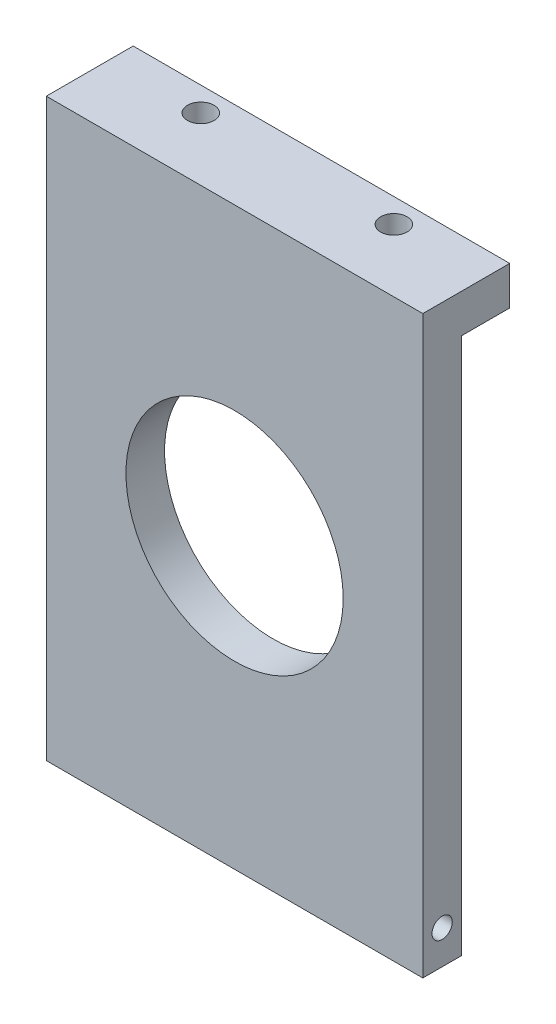
SolidWorks part; units mm, degrees
ref_plane "前视基准面" through (0, 0, 0) normal (0, 0, 1) x (1, 0, 0)
ref_plane "上视基准面" through (0, 0, 0) normal (0, 1, 0) x (1, 0, 0)
ref_plane "右视基准面" through (0, 0, 0) normal (1, 0, 0) x (0, 0, -1)
sketch "草图1" plane through (0, 0, 0) normal (0, 0, 1) x (1, 0, 0)
  line L0 (0, 119.63) -> (-78, 119.63)
  line L1 (0, 0) -> (0, 119.63)
  line L2 (-78, 0) -> (0, 0)
  line L3 (-78, 119.63) -> (-78, 0)
  line L38 (-63.75, 59.815) -> (-14.25, 59.815) construction
  line L39 (-39, 35.065) -> (-39, 84.565) construction
  circle A0 centre (-39, 59.815) radius 22.5
extrude "凸台-拉伸1" add sketch "草图1" along normal blind 8
hole_wizard "M5 螺纹孔1" positions "草图2" profile "草图3" tap size "M5" standard "ISO"
sketch "草图2" plane through (0, 119.63, 0) normal (0, 1, 0) x (1, 0, 0)
  line L0 (-39, 0) -> (-39, -8) construction
  line L1 (0, 0) -> (-78, 0) construction
  line L2 (0, -8) -> (-78, -8) construction
  point P0 (-68, -4)
  point P2 (-10, -4)
  dimension "D1" = 4
  dimension "D2" = 58
sketch "草图3" plane through (-68, 119.63, 4) normal (1, 0, 0) x (0, 0, 1)
  line L0 (0, 0) -> (0, 13.6618)
  line L1 (0, 13.6618) -> (2.1, 12.4)
  line L2 (2.1, 12.4) -> (2.1, 0)
  line L5 (2.1, 0) -> (0, 0)
  line L10 (0, 13.6618) -> (-2.1, 12.4) construction
  line L11 (0, -6.35) -> (0, 107.95) construction
  dimension "螺纹孔钻头直径" = 4.2
  dimension "螺纹孔钻头深度" = 12.4
  dimension "导头角度" = 118
cosmetic thread "孔螺蚊线1" parameters "D1"=10, "D2"=5
cosmetic thread "孔螺蚊线2" parameters "D1"=10, "D2"=5
ref_plane "基准面2" through (0, 59.815, 0) normal (0, 1, 0) x (1, 0, 0)
mirror "镜向1" about plane through (0, 59.815, 0) normal (0, 1, 0) of "M5 螺纹孔1"
sketch "草图4" plane through (0, 0, 8) normal (0, 0, 1) x (1, 0, 0)
  line L0 (-78, 119.63) -> (-78, 0) construction
  line L1 (0, 119.63) -> (-78, 119.63)
  line L2 (0, 119.63) -> (0, 96.1061)
  line L3 (0, 96.1061) -> (-78, 96.1061)
  line L4 (-78, 119.63) -> (-78, 96.1061)
extrude "凸台-拉伸2" add sketch "草图4" against normal up to surface (8 mm away) up to face at (-39, 59.815, 0)
sketch "草图5" plane through (0, 0, 0) normal (0, 0, -1) x (-1, 0, 0)
  line L0 (0, 0) -> (0, 119.63) construction
  line L1 (78, 119.63) -> (0, 119.63)
  line L2 (78, 119.63) -> (78, 111.2)
  line L3 (78, 111.2) -> (0, 111.2)
  line L4 (0, 119.63) -> (0, 111.2)
  dimension "D1" = 8.43
extrude "凸台-拉伸3" add sketch "草图5" along normal blind 10
sketch "草图6" plane through (0, 119.63, 0) normal (0, 1, 0) x (1, 0, 0)
  line L1 (-78, 10) -> (0, 10)
  line L2 (-78, 10) -> (-78, -8)
  line L3 (-78, -8) -> (0, -8)
  line L4 (0, 10) -> (0, -8)
extrude "切除-拉伸1" cut sketch "草图6" against normal blind 0.43
sketch "草图7" plane through (0, 111.2, 0) normal (0, -1, 0) x (1, 0, 0)
  line L0 (-78, -5) -> (0, -5) construction
  line L1 (-78, -10) -> (-78, 0) construction
  line L2 (0, -10) -> (0, 0) construction
  line L3 (0, -5) -> (-39, -5) construction
  line L4 (-39, -5) -> (-39, 0) construction
  line L5 (0, 0) -> (-78, 0) construction
  circle A0 centre (-59, -5) radius 2.75
  circle A1 centre (-19, -5) radius 2.75
  dimension "D1" = 5.5
  dimension "D2" = 40
extrude "切除-拉伸2" cut sketch "草图7" against normal through all
hole_wizard "M5 螺纹孔2" positions "草图8" profile "草图9" tap size "M5" standard "ISO"
sketch "草图8" plane through (-78, 0, 0) normal (-1, 0, 0) x (0, 0, 1)
  point P0 (4, 7)
  point P3 (-86, 7)
sketch "草图9" plane through (-78, 7, 4) normal (0, 1, 0) x (0, 0, 1)
  line L0 (0, 0) -> (0, 7.2618)
  line L1 (0, 7.2618) -> (2.1, 6)
  line L2 (2.1, 6) -> (2.1, 0)
  line L5 (2.1, 0) -> (0, 0)
  line L10 (0, 7.2618) -> (-2.1, 6) construction
  line L11 (0, -6.35) -> (0, 107.95) construction
  dimension "螺纹孔钻头直径" = 4.2
  dimension "螺纹孔钻头深度" = 6
  dimension "导头角度" = 118
cosmetic thread "孔螺蚊线3" parameters "D1"=6, "D2"=5
ref_plane "基准面3" through (-39, 0, 0) normal (1, 0, 0) x (0, 0, -1)
mirror "镜向2" about plane through (-39, 0, 0) normal (1, 0, 0) of "M5 螺纹孔2"
